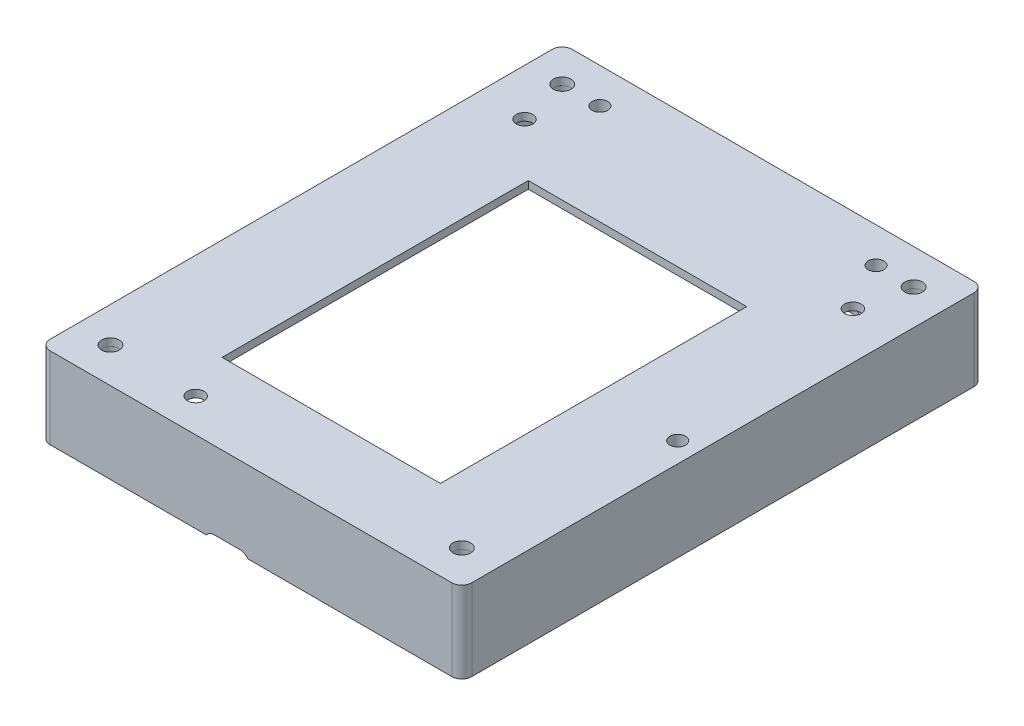
SolidWorks part; units mm, degrees
ref_plane "前视基准面" through (0, 0, 0) normal (0, 0, 1) x (1, 0, 0)
ref_plane "上视基准面" through (0, 0, 0) normal (0, 1, 0) x (1, 0, 0)
ref_plane "右视基准面" through (0, 0, 0) normal (1, 0, 0) x (0, 0, -1)
other "Configuration Table"
sketch "草图1" plane through (0, 0, 0) normal (0, 1, 0) x (1, 0, 0)
  line L1 (-40.5, 50.5) -> (40.5, 50.5)
  line L2 (-40.5, 50.5) -> (-40.5, -50.5)
  line L3 (-40.5, -50.5) -> (40.5, -50.5)
  line L4 (40.5, 50.5) -> (40.5, -50.5)
  line L5 (-40.5, 50.5) -> (40.5, -50.5) construction
  line L6 (-40.5, -50.5) -> (40.5, 50.5) construction
  line L7 (-40, 52) -> (40, 52)
  line L8 (-42, 50) -> (-42, -50)
  line L9 (-40, -52) -> (40, -52)
  line L10 (42, 50) -> (42, -50)
  line L11 (-42, 52) -> (42, -52) construction
  line L12 (-42, -52) -> (42, 52) construction
  arc A0 (-40, 52) -> (-42, 50) centre (-40, 50) ccw
  arc A2 (-42, -50) -> (-40, -52) centre (-40, -50) ccw
  arc A3 (40, -52) -> (42, -50) centre (40, -50) ccw
  arc A4 (42, 50) -> (40, 52) centre (40, 50) ccw
  point P0 (0, 0)
  point P6 (0, 0)
  dimension "D5" = 4
  dimension "D7" = 4
  dimension "D8" = 4
  dimension "D1" = 81
  dimension "D2" = 84
  dimension "D3" = 101
  dimension "D4" = 104
extrude "凸台-拉伸1" add sketch "草图1" along normal blind 16.2
sketch "草图2" plane through (0, 16.2, 0) normal (0, 1, 0) x (1, 0, 0)
  line L0 (40.5, 50.5) -> (-40.5, 50.5) construction
  line L1 (40.5, 50.5) -> (-40.5, 50.5)
  line L2 (-40.5, -50.5) -> (40.5, -50.5) construction
  line L3 (40.5, -50.5) -> (40.5, 50.5) construction
  line L4 (-40.5, 50.5) -> (-40.5, -50.5) construction
  line L5 (-40.5, -50.5) -> (40.5, -50.5)
  line L6 (40.5, -50.5) -> (40.5, 50.5)
  line L7 (-40.5, 50.5) -> (-40.5, -50.5)
extrude "凸台-拉伸2" add sketch "草图2" against normal blind 1.5
sketch "草图3" plane through (0, 16.2, 0) normal (0, 1, 0) x (1, 0, 0)
  line L0 (-40, -52) -> (40, -52) construction
  line L1 (21.75, -36) -> (-21.75, -36)
  line L2 (21.75, -36) -> (21.75, 25)
  line L3 (21.75, 25) -> (-21.75, 25)
  line L4 (-21.75, -36) -> (-21.75, 25)
  line L5 (21.75, -36) -> (-21.75, 25) construction
  line L6 (21.75, 25) -> (-21.75, -36) construction
  line L7 (42, -50) -> (42, 50) construction
  line L11 (40, 52) -> (-40, 52) construction
  line L12 (-42, 50) -> (-42, -50) construction
  circle A0 centre (-32.7, 35.2) radius 1.65
  circle A1 centre (-17.7, -45.3) radius 1.65
  circle A2 centre (32.7, 35.2) radius 1.65
  point P0 (0, -5.5)
  dimension "D7" = 3.3
  dimension "D14" = 3.3
  dimension "D9" = 9.3
  dimension "D10" = 3.3
  dimension "D1" = 43.5
  dimension "D2" = 16
  dimension "D3" = 20.25
  dimension "D4" = 61
  dimension "D5" = 16.8
  dimension "D6" = 9.3
  dimension "D8" = 16.8
  dimension "D12" = 24.3
  dimension "D13" = 6.7
extrude "切除-拉伸1" cut sketch "草图3" against normal blind 1.5
sketch "草图4" plane through (0, 16.2, 0) normal (0, 1, 0) x (1, 0, 0)
  line L0 (-42, 50) -> (-42, -50) construction
  line L1 (42, -50) -> (42, 50) construction
  line L2 (-40, -52) -> (40, -52) construction
  line L4 (40, 52) -> (-40, 52) construction
  circle A0 centre (35, 45) radius 1.75
  circle A1 centre (-35, 45) radius 1.75
  circle A2 centre (-35, -45) radius 1.75
  circle A3 centre (35, -45) radius 1.75
  dimension "D3" = 7
  dimension "D4" = 7
  dimension "D5" = 3.5
  dimension "D6" = 3.5
  dimension "D7" = 3.5
  dimension "D8" = 3.5
  dimension "D1" = 7
  dimension "D2" = 7
extrude "切除-拉伸2" cut sketch "草图4" against normal blind 1.5
sketch "草图5" plane through (0, 0, 52) normal (0, 0, 1) x (1, 0, 0)
  line L0 (-7.31, -1.2) -> (-2.21, -1.2) construction
  line L1 (-7.31, 0.8) -> (-2.21, 0.8)
  line L2 (-7.31, -3.2) -> (-2.21, -3.2)
  line L3 (-40, 0) -> (40, 0) construction
  line L5 (-42, 16.2) -> (-42, 0) construction
  arc A0 (-7.31, 0.8) -> (-7.31, -3.2) centre (-7.31, -1.2) ccw
  arc A1 (-2.21, -3.2) -> (-2.21, 0.8) centre (-2.21, -1.2) ccw
  point P2 (-4.76, -1.2)
  dimension "D1" = 2
  dimension "D3" = 34.69
  dimension "D2" = 3.2
  dimension "D4" = 39.79
extrude "切除-拉伸3" cut sketch "草图5" against normal blind 1.5
sketch "草图6" plane through (0, 14.7, 0) normal (0, -1, 0) x (1, 0, 0)
  circle A0 centre (35, -45) radius 1.75 construction
  circle A1 centre (-35, -45) radius 1.75 construction
  circle A2 centre (-35, 45) radius 1.75 construction
  circle A3 centre (35, 45) radius 1.75 construction
  circle A4 centre (35, -45) radius 1.75
  circle A5 centre (-35, -45) radius 1.75
  circle A6 centre (-35, 45) radius 1.75
  circle A7 centre (35, 45) radius 1.75
  circle A8 centre (-35, 45) radius 2.25
  circle A9 centre (35, 45) radius 2.25
  circle A10 centre (-35, -45) radius 2.25
  circle A11 centre (35, -45) radius 2.25
  dimension "D1" = 4.5
  dimension "D2" = 4.5
  dimension "D3" = 4.5
  dimension "D4" = 4.5
extrude "凸台-拉伸3" add sketch "草图6" along normal offset from surface (13.1 mm away) 1.6 separate body up to face at (-1.19, 0, 12.8125)
sketch "草图7" plane through (0, 0, -52) normal (0, 0, -1) x (-1, 0, 0)
  line L0 (42, 16.2) -> (42, 0) construction
  line L1 (10, 7.5) -> (23, 7.5)
  line L2 (10, 7.5) -> (10, 1.5)
  line L3 (10, 1.5) -> (23, 1.5)
  line L4 (23, 7.5) -> (23, 1.5)
  line L5 (-40, 0) -> (40, 0) construction
  dimension "D1" = 19
  dimension "D2" = 13
  dimension "D3" = 6
  dimension "D4" = 1.5
extrude "切除-拉伸4" cut sketch "草图7" against normal up to next (1.5 mm away)
sketch "草图8" plane through (0, 16.2, 0) normal (0, 1, 0) x (1, 0, 0)
  line L0 (42, -50) -> (42, 50) construction
  circle A0 centre (-27.5, 45) radius 1.55
  circle A1 centre (27.5, 45) radius 1.55
  circle A2 centre (35, 45) radius 1.75 construction
  circle A3 centre (38, -5) radius 1.55
  dimension "D1" = 3.1
  dimension "D2" = 3.1
  dimension "D3" = 55
  dimension "D6" = 3.1
  dimension "D4" = 27.5
  dimension "D5" = 50
  dimension "D7" = 4
extrude "切除-拉伸5" cut sketch "草图8" against normal through all
sketch "草图9" plane through (0, 14.7, 0) normal (0, -1, 0) x (1, 0, 0)
  circle A0 centre (27.5, -45) radius 1.55 construction
  circle A1 centre (-27.5, -45) radius 1.55 construction
  circle A2 centre (27.5, -45) radius 1.55
  circle A3 centre (-27.5, -45) radius 1.55
  circle A4 centre (-27.5, -45) radius 2.3588
  circle A5 centre (27.5, -45) radius 2.5232
  circle A6 centre (38, 5) radius 1.55 construction
  circle A7 centre (38, 5) radius 1.55
  circle A8 centre (38, 5) radius 2.525
  dimension "D1" = 5.05
extrude "凸台-拉伸4" add sketch "草图9" along normal blind 5
sketch "草图10" plane through (0, 9.7, 0) normal (0, -1, 0) x (1, 0, 0)
  line L0 (40.5, 5.3544) -> (40.5, 4.6456)
  circle A0 centre (-27.5, -45) radius 2.3588 construction
  circle A1 centre (27.5, -45) radius 2.5232
  circle A2 centre (27.5, -45) radius 2.5232
  circle A3 centre (-27.5, -45) radius 2.3588
  arc A4 (40.5, 5.3544) -> (40.5, 4.6456) centre (38, 5) ccw construction
  arc A5 (40.5, 5.3544) -> (40.5, 4.6456) centre (38, 5) ccw
  dimension "D1" = 0
extrude "凸台-拉伸5" add sketch "草图10" along normal blind 1.5
